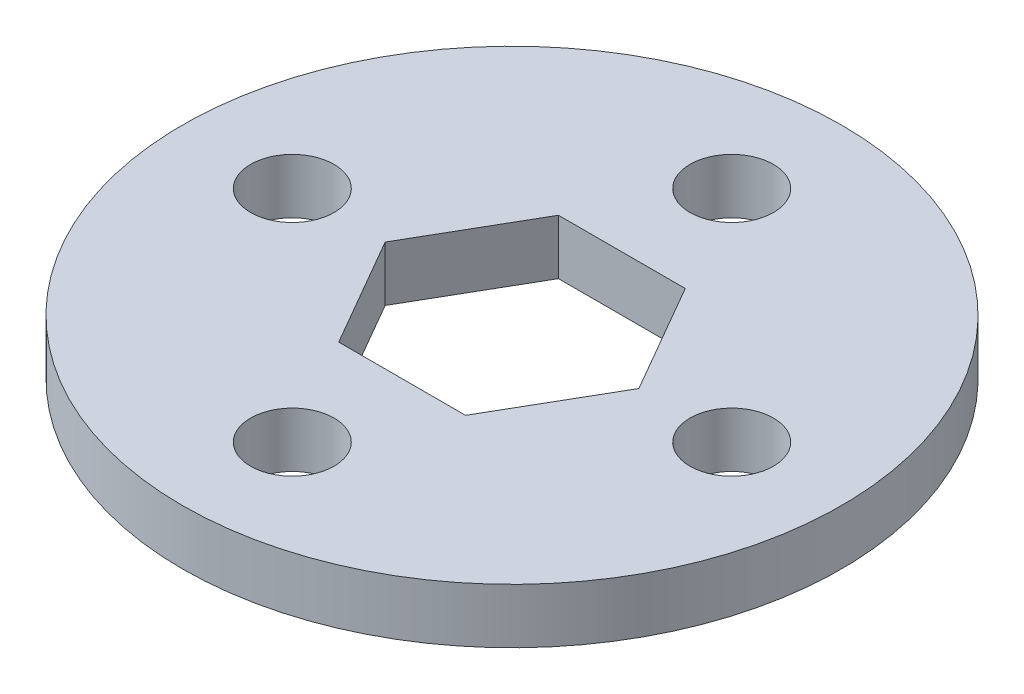
SolidWorks part; units mm, degrees
ref_plane "Front Plane" through (0, 0, 0) normal (0, 0, 1) x (1, 0, 0)
ref_plane "Top Plane" through (0, 0, 0) normal (0, 1, 0) x (1, 0, 0)
ref_plane "Right Plane" through (0, 0, 0) normal (1, 0, 0) x (0, 0, -1)
sketch "Sketch1" plane through (0, 0, 0) normal (0, 1, 0) x (1, 0, 0)
  line L0 (0, 19.05) -> (0, 6.35) construction
  line L1 (-7.3323, 0) -> (-3.6662, -6.35)
  line L2 (-3.6662, -6.35) -> (3.6662, -6.35)
  line L3 (3.6662, -6.35) -> (7.3323, 0)
  line L4 (7.3323, 0) -> (3.6662, 6.35)
  line L5 (3.6662, 6.35) -> (-3.6662, 6.35)
  line L6 (-3.6662, 6.35) -> (-7.3323, 0)
  circle A0 centre (0, 0) radius 19.05
  circle A1 centre (0, 0) radius 6.35 construction
  circle A2 centre (0, 12.7) radius 2.413
  circle A3 centre (12.7, 0) radius 2.413
  circle A4 centre (0, -12.7) radius 2.413
  circle A5 centre (-12.7, 0) radius 2.413
  point P14 (0, 0)
  point P15 (0, 0)
  point P23 (0, 0)
  dimension "D2" = 38.1
  dimension "D3" = 4.826
  dimension "D1" = 12.7
  dimension "D4" = 4
extrude "Boss-Extrude1" add sketch "Sketch1" along normal blind 3.175
